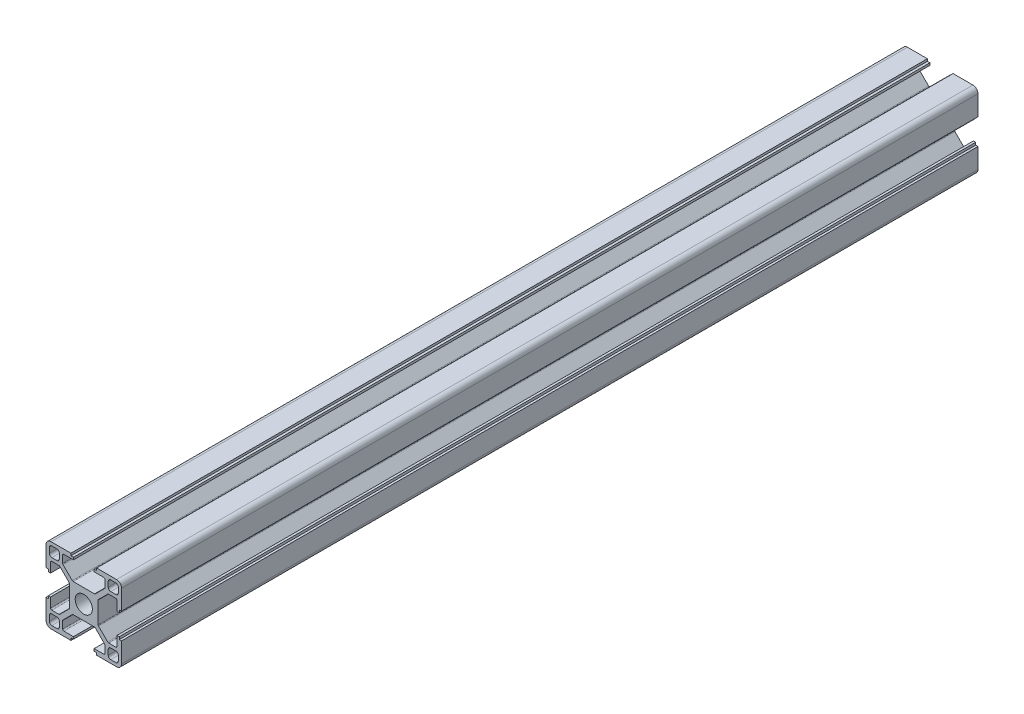
SolidWorks part; units mm, degrees
ref_plane "前视基准面" through (0, 0, 0) normal (0, 0, 1) x (1, 0, 0)
ref_plane "上视基准面" through (0, 0, 0) normal (0, 1, 0) x (1, 0, 0)
ref_plane "右视基准面" through (0, 0, 0) normal (1, 0, 0) x (0, 0, -1)
sketch "草图1" plane through (0, 0, 0) normal (0, 0, 1) x (1, 0, 0)
  line L0 (0, 0) -> (0, 65.3905) construction
  line L1 (0, 0) -> (64.2648, 0) construction
  line L2 (0, 0) -> (79.9729, 79.9729) construction
  line L3 (5.7, 0) -> (5.7, 4.4272)
  line L4 (5.7, 4.4272) -> (9.6728, 8.4)
  line L5 (9.6728, 8.4) -> (13.2, 8.4)
  line L6 (13.2, 8.4) -> (13.2, 4.1)
  line L7 (13.2, 4.1) -> (14.1, 4.1)
  line L8 (14.1, 4.1) -> (14.1, 5.1)
  line L9 (14.1, 5.1) -> (15, 5.1)
  line L10 (15, 5.1) -> (15, 15)
  line L11 (5.1, 15) -> (15, 15)
  line L12 (5.1, 14.1) -> (5.1, 15)
  line L13 (4.1, 14.1) -> (5.1, 14.1)
  line L14 (4.1, 13.2) -> (4.1, 14.1)
  line L15 (8.4, 13.2) -> (4.1, 13.2)
  line L16 (8.4, 9.6728) -> (8.4, 13.2)
  line L17 (4.4272, 5.7) -> (8.4, 9.6728)
  line L18 (0, 5.7) -> (4.4272, 5.7)
  line L20 (9.7, 9.7) -> (13.7, 9.7)
  line L21 (9.7, 9.7) -> (9.7, 13.7)
  line L22 (9.7, 13.7) -> (13.7, 13.7)
  line L23 (13.7, 9.7) -> (13.7, 13.7)
  line L24 (9.7, 9.7) -> (13.7, 13.7) construction
  line L25 (9.7, 13.7) -> (13.7, 9.7) construction
  line L26 (0, 5.7) -> (0, 0)
  line L27 (0, 0) -> (5.7, 0)
  point P9 (11.7, 11.7)
  dimension "D1" = 45
  dimension "D2" = 5.7
  dimension "D3" = 1.8
  dimension "D4" = 0.9
  dimension "D5" = 8.2
  dimension "D6" = 10.2
  dimension "D7" = 1.8
  dimension "D8" = 15
  dimension "D9" = 16.8
  dimension "D10" = 4
  dimension "D11" = 1.3
extrude "凸台-拉伸1" add sketch "草图1" along normal blind 340 contours L3 L4 L5 L6 L7 L8 L9 L10 L11 L12 L13 L14 L15 L16 L17 L18 L26 L27
fillet "圆角1" radius 1 4 edges at (9.7, 9.7, 170) (13.7, 9.7, 170) (9.7, 13.7, 170) (13.7, 13.7, 170)
fillet "圆角2" radius 2 1 edges at (15, 15, 170)
fillet "圆角3" radius 0.5 6 edges at (5.7, 4.4272, 170) (4.4272, 5.7, 170) (8.4, 13.2, 170) (8.4, 9.6728, 170) (9.6728, 8.4, 170) (13.2, 8.4, 170)
pattern_circular "阵列(圆周)1" count 4 over 360 about axis through (0, 0, 0) along (0, 0, 1) of "圆角2", "圆角3", "凸台-拉伸1", "圆角1"
sketch "草图2" plane through (0, 0, 340) normal (0, 0, 1) x (1, 0, 0)
  circle A0 centre (0, 0) radius 3.4
  dimension "D1" = 6.8
extrude "切除-拉伸1" cut sketch "草图2" against normal through all
cosmetic thread "装饰螺纹线1" parameters "D1"=20, "D2"=8
cosmetic thread "装饰螺纹线2" parameters "D1"=20, "D2"=8
sketch "草图3" plane through (0, 0, 0) normal (1, 0, 0) x (0, 0, -1)
  line L0 (-170, 60.2652) -> (-170, -70.1349) construction
  line L1 (-318.169, 0) -> (51.4974, 0) construction
  line L2 (0, 5.1) -> (0, 13) construction
  line L3 (-340, 5.1) -> (-340, 13) construction
  circle A1 centre (-185, 0) radius 3.15
  circle A2 centre (-155, 0) radius 3.15
  dimension "D1" = 6.3
  dimension "D2" = 30
extrude "切除-拉伸2" cut sketch "草图3" against normal mid plane 20
